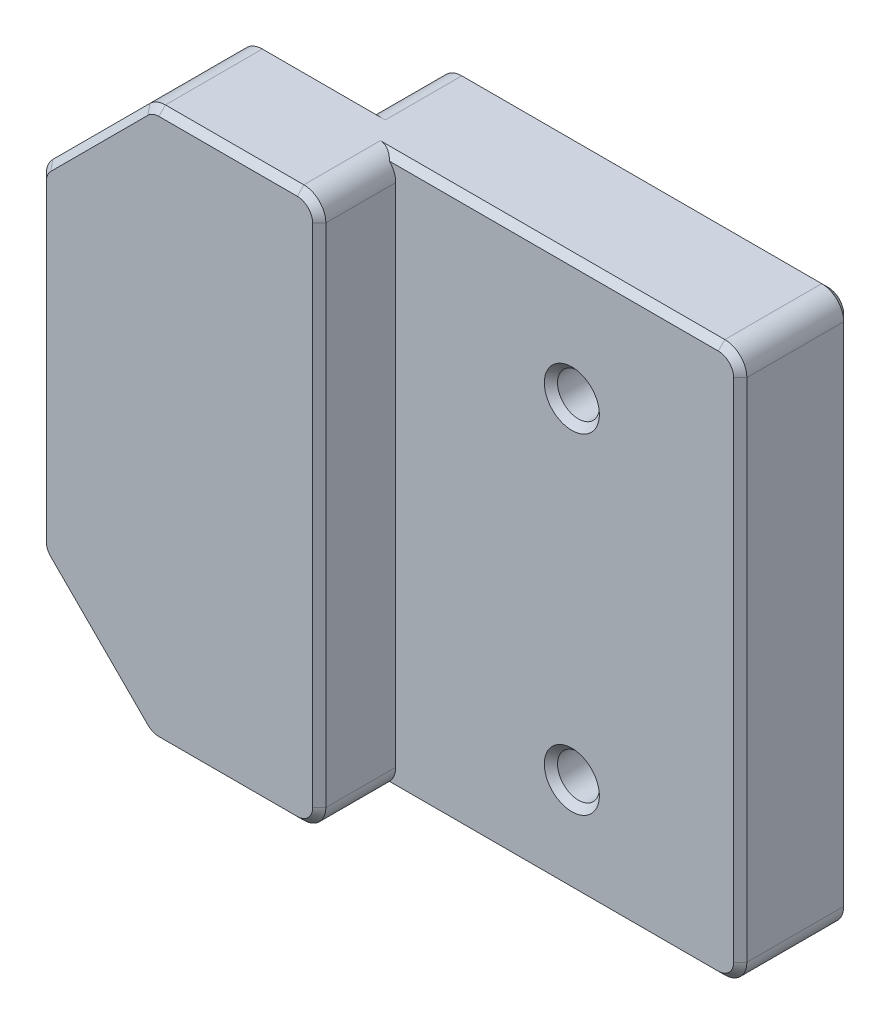
SolidWorks part; units mm, degrees
ref_plane "Front Plane" through (0, 0, 0) normal (0, 0, 1) x (1, 0, 0)
ref_plane "Top Plane" through (0, 0, 0) normal (0, 1, 0) x (1, 0, 0)
ref_plane "Right Plane" through (0, 0, 0) normal (1, 0, 0) x (0, 0, -1)
sketch "Sketch1" plane through (0, 0, 0) normal (0, 1, 0) x (1, 0, 0)
  line L0 (0, 0) -> (-18.35, 0)
  line L1 (-18.35, 0) -> (-18.35, -3.475)
  line L2 (-18.35, -3.475) -> (-28.35, -3.475)
  line L3 (-28.35, -3.475) -> (-28.35, -8.475)
  line L4 (-28.35, -8.475) -> (-15.65, -8.475)
  line L5 (-15.65, -8.475) -> (-15.65, -5)
  line L6 (-15.65, -5) -> (0, -5)
  line L7 (0, -5) -> (0, 0)
  dimension "D1" = 5
  dimension "D2" = 2.7
  dimension "D3" = 18.35
  dimension "D4" = 10
  dimension "D5" = 3.475
  dimension "D6" = 5
extrude "Boss-Extrude1" add sketch "Sketch1" along normal blind 25
sketch "Sketch2" plane through (0, 0, 5) normal (0, 0, 1) x (1, 0, 0)
  line L0 (-7.65, 4.5) -> (-7.65, 19.5) construction
  line L1 (-15.65, 0) -> (0, 0) construction
  line L2 (0, 25) -> (0, 0) construction
  circle A0 centre (-7.65, 4.5) radius 0.95
  circle A1 centre (-7.65, 19.5) radius 0.95
  dimension "D1" = 1.9
  dimension "D2" = 4.5
  dimension "D3" = 7.65
  dimension "D4" = 15
extrude "Cut-Extrude1" cut sketch "Sketch2" against normal blind 25
chamfer "Chamfer1" distance 5 angle 45 2 edges at (-28.35, 0, 5.975) (-28.35, 25, 5.975)
fillet "Fillet1" radius 1 10 edges at (0, 0, 2.5) (-28.35, 20, 5.975) (-15.65, 25, 6.7375) (-15.65, 0, 6.7375) (-23.35, 0, 5.975) (-28.35, 5, 5.975) (-23.35, 25, 5.975) (0, 25, 2.5) (-18.35, 25, 1.7375) (-18.35, 0, 1.7375)
chamfer "Chamfer2" distance 0.3 angle 45 38 edges at (-6.7, 4.5, 0) (-6.7, 19.5, 0) (-6.7, 4.5, 5) (-6.7, 19.5, 5) (-9.175, 0, 0) (-0.2929, 0.2929, 0) (0, 12.5, 0) (-0.2929, 24.7071, 0) (-9.175, 25, 0) (-28.35, 12.5, 8.475) (-28.2739, 19.9685, 8.475) (-28.2739, 5.0315, 8.475) (-25.85, 22.5, 8.475) (-25.85, 2.5, 8.475) (-23.3185, 24.9239, 8.475) (-23.3185, 0.0761, 8.475) (-19.7929, 25, 8.475) (-19.7929, 0, 8.475) (-15.9429, 24.7071, 8.475) (-15.9429, 0.2929, 8.475) (-15.65, 12.5, 8.475) (-18.0571, 0.2929, 0) (-18.35, 12.5, 0) (-18.0571, 24.7071, 0) (-8.825, 25, 5) (-8.825, 0, 5) (-0.2929, 24.7071, 5) (-0.2929, 0.2929, 5) (0, 12.5, 5) (-20.1429, 0, 3.475) (-23.3185, 0.0761, 3.475) (-25.85, 2.5, 3.475) (-28.2739, 5.0315, 3.475) (-28.35, 12.5, 3.475) (-20.1429, 25, 3.475) (-28.2739, 19.9685, 3.475) (-23.3185, 24.9239, 3.475) (-25.85, 22.5, 3.475)
